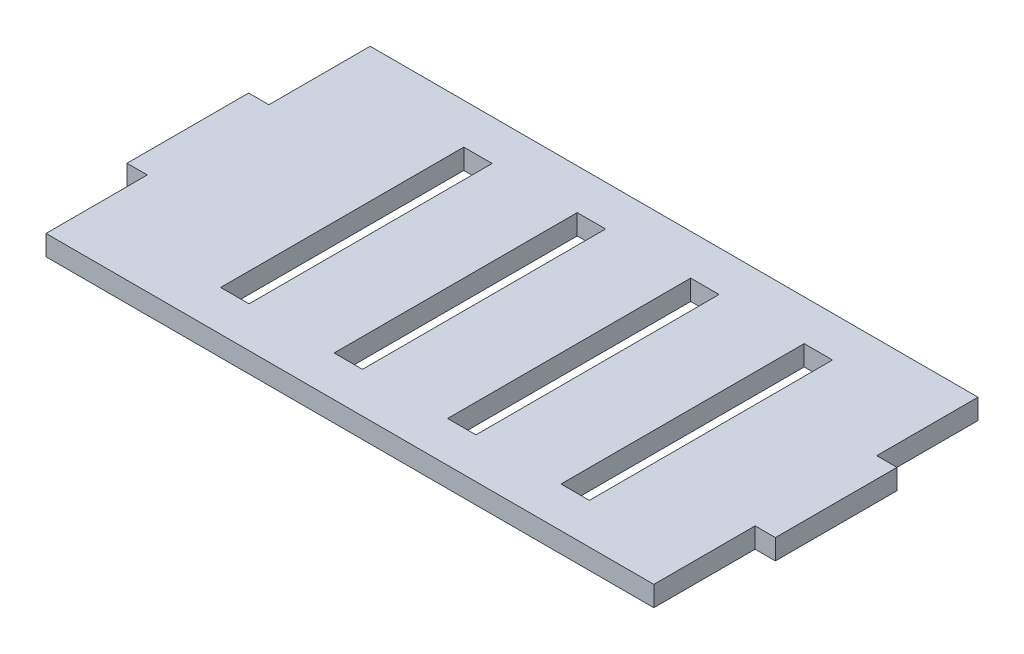
SolidWorks part; units mm, degrees
other "tab2"
ref_plane "Front Plane" through (0, 0, 0) normal (0, 0, 1) x (1, 0, 0)
ref_plane "Top Plane" through (0, 0, 0) normal (0, 1, 0) x (1, 0, 0)
ref_plane "Right Plane" through (0, 0, 0) normal (1, 0, 0) x (0, 0, -1)
sketch "Sketch1" plane through (0, 0, 0) normal (0, 1, 0) x (1, 0, 0)
  line L1 (-95.25, -50.8) -> (95.25, -50.8)
  line L2 (-95.25, -50.8) -> (-95.25, 50.8)
  line L3 (-95.25, 50.8) -> (95.25, 50.8)
  line L4 (95.25, -50.8) -> (95.25, 50.8)
  line L5 (-95.25, -50.8) -> (95.25, 50.8) construction
  line L6 (-95.25, 50.8) -> (95.25, -50.8) construction
  point P0 (0, 0)
  dimension "D1" = 190.5
  dimension "D2" = 101.6
extrude "Boss-Extrude1" add sketch "Sketch1" along normal blind 6.35
sketch "Sketch2" plane through (0, 6.35, 0) normal (0, 1, 0) x (1, 0, 0)
  line L0 (-3.4926, 0) -> (3.4926, 0) construction
  line L1 (-53.213, 38.1) -> (-44.323, 38.1)
  line L2 (-53.213, 38.1) -> (-53.213, -38.1)
  line L3 (-53.213, -38.1) -> (-44.323, -38.1)
  line L4 (-44.323, 38.1) -> (-44.323, -38.1)
  line L5 (-53.213, 38.1) -> (-44.323, -38.1) construction
  line L6 (-53.213, -38.1) -> (-44.323, 38.1) construction
  line L8 (-17.653, 38.1) -> (-8.763, 38.1)
  line L9 (-17.653, 38.1) -> (-17.653, -38.1)
  line L10 (-17.653, -38.1) -> (-8.763, -38.1)
  line L11 (-8.763, 38.1) -> (-8.763, -38.1)
  line L12 (-17.653, 38.1) -> (-8.763, -38.1) construction
  line L13 (-17.653, -38.1) -> (-8.763, 38.1) construction
  line L14 (17.907, 38.1) -> (26.797, 38.1)
  line L15 (17.907, 38.1) -> (17.907, -38.1)
  line L16 (17.907, -38.1) -> (26.797, -38.1)
  line L17 (26.797, 38.1) -> (26.797, -38.1)
  line L18 (17.907, 38.1) -> (26.797, -38.1) construction
  line L19 (17.907, -38.1) -> (26.797, 38.1) construction
  line L20 (53.467, 38.1) -> (62.357, 38.1)
  line L21 (53.467, 38.1) -> (53.467, -38.1)
  line L22 (53.467, -38.1) -> (62.357, -38.1)
  line L23 (62.357, 38.1) -> (62.357, -38.1)
  line L24 (53.467, 38.1) -> (62.357, -38.1) construction
  line L25 (53.467, -38.1) -> (62.357, 38.1) construction
  line L26 (-48.768, 0) -> (-13.208, 0) construction
  line L27 (-95.25, 50.8) -> (-95.25, -50.8) construction
  point P0 (-48.768, 0)
  point P10 (-13.208, 0)
  point P15 (22.352, 0)
  point P20 (57.912, 0)
  dimension "D1" = 8.89
  dimension "D2" = 76.2
  dimension "D3" = 46.482
  dimension "D5" = 35.56
  dimension "D4" = 4
extrude "hole" cut sketch "Sketch2" against normal blind 6.35
sketch "Sketch3" plane through (-95.25, 0, 0) normal (-1, 0, 0) x (0, 0, 1)
  line L0 (-50.8, 6.35) -> (50.8, 6.35) construction
  line L1 (-19.05, 6.35) -> (19.05, 6.35)
  line L2 (-19.05, 6.35) -> (-19.05, 0)
  line L3 (-19.05, 0) -> (19.05, 0)
  line L4 (19.05, 6.35) -> (19.05, 0)
  line L5 (-50.8, 0) -> (50.8, 0) construction
  line L6 (-50.8, 6.35) -> (-50.8, 0) construction
  line L7 (50.8, 6.35) -> (50.8, 0) construction
  point P8 (-50.8, 3.175)
  dimension "D1" = 31.75
  dimension "D2" = 31.75
extrude "tab1" add sketch "Sketch3" along normal blind 6.35
sketch "Sketch4" plane through (95.25, 0, 0) normal (1, 0, 0) x (0, 0, -1)
  line L0 (-50.8, 6.35) -> (50.8, 6.35) construction
  line L1 (-19.05, 6.35) -> (19.05, 6.35)
  line L2 (-19.05, 6.35) -> (-19.05, 0)
  line L3 (-19.05, 0) -> (19.05, 0)
  line L4 (19.05, 6.35) -> (19.05, 0)
  line L5 (-50.8, 0) -> (50.8, 0) construction
  line L6 (-50.8, 6.35) -> (-50.8, 0) construction
  line L7 (50.8, 6.35) -> (50.8, 0) construction
  dimension "D1" = 31.75
  dimension "D2" = 31.75
extrude "tab2" add sketch "Sketch4" along normal blind 6.35
